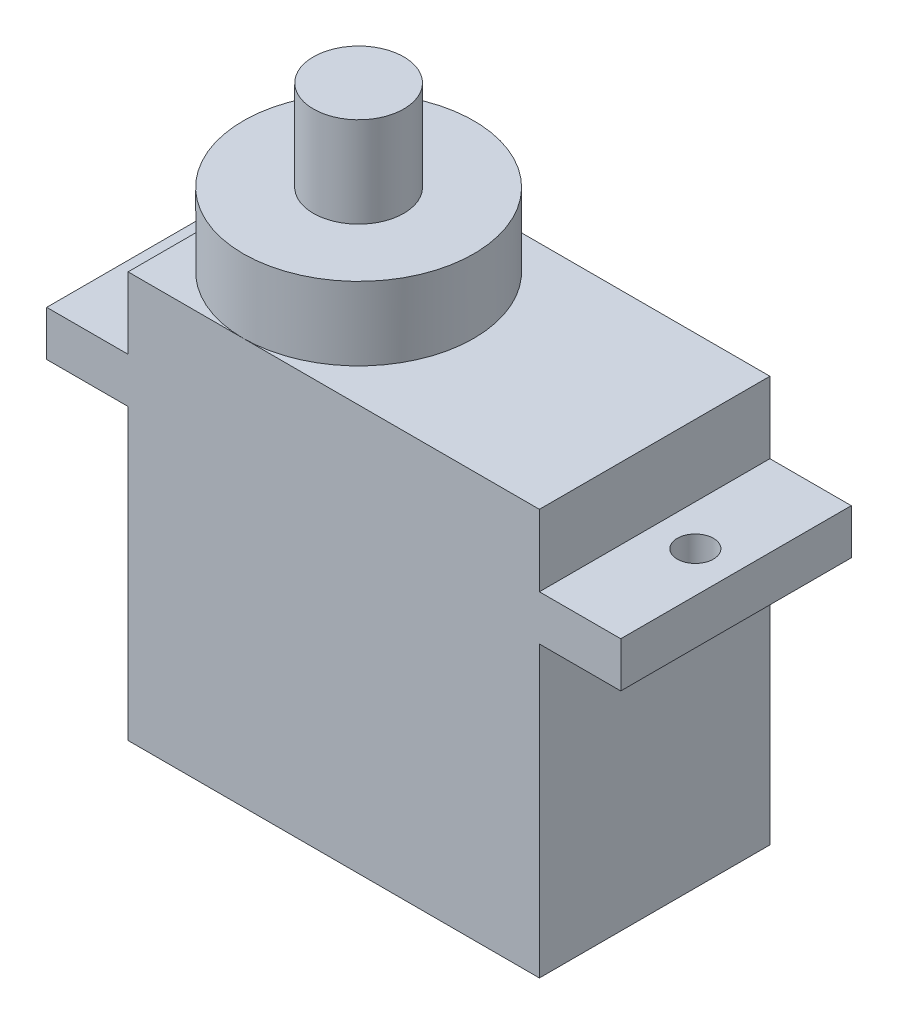
SolidWorks part; units mm, degrees
ref_plane "Front Plane" through (0, 0, 0) normal (0, 0, 1) x (1, 0, 0)
ref_plane "Top Plane" through (0, 0, 0) normal (0, 1, 0) x (1, 0, 0)
ref_plane "Right Plane" through (0, 0, 0) normal (1, 0, 0) x (0, 0, -1)
sketch "Sketch1" plane through (0, 0, 0) normal (0, 0, 1) x (1, 0, 0)
  line L1 (-7.8959, -11.225) -> (14.8541, -11.225)
  line L2 (-7.8959, -11.225) -> (-7.8959, 11.225)
  line L3 (-7.8959, 11.225) -> (14.8541, 11.225)
  line L4 (14.8541, -11.225) -> (14.8541, 11.225)
  point P0 (0, 0)
  dimension "D1" = 22.45
  dimension "D2" = 22.75
extrude "Boss-Extrude1" add sketch "Sketch1" along normal blind 12.75
sketch "Sketch2" plane through (14.8541, 0, 0) normal (1, 0, 0) x (0, 0, -1)
  line L0 (-12.75, -11.225) -> (-12.75, 11.225) construction
  line L1 (-12.75, 7.275) -> (0, 7.275)
  line L2 (-12.75, 7.275) -> (-12.75, 4.775)
  line L3 (-12.75, 4.775) -> (0, 4.775)
  line L4 (0, 7.275) -> (0, 4.775)
  line L5 (0, -11.225) -> (0, 11.225) construction
  line L6 (-12.75, -11.225) -> (0, -11.225) construction
  dimension "D1" = 2.5
  dimension "D2" = 18.5
extrude "Boss-Extrude2" add sketch "Sketch2" along normal blind 4.5
sketch "Sketch3" plane through (-7.8959, 0, 0) normal (-1, 0, 0) x (0, 0, 1)
  line L0 (0, 11.225) -> (0, -11.225) construction
  line L1 (0, 7.275) -> (12.75, 7.275)
  line L2 (0, 7.275) -> (0, 4.775)
  line L3 (0, 4.775) -> (12.75, 4.775)
  line L4 (12.75, 7.275) -> (12.75, 4.775)
  line L5 (12.75, 11.225) -> (12.75, -11.225) construction
  line L6 (12.75, -11.225) -> (0, -11.225) construction
  dimension "D1" = 2.5
  dimension "D2" = 18.5
extrude "Boss-Extrude3" add sketch "Sketch3" along normal blind 4.5
sketch "Sketch4" plane through (0, 7.275, 0) normal (0, 1, 0) x (1, 0, 0)
  line L1 (-12.3959, 0) -> (-7.8959, 0) construction
  line L3 (-12.3959, -12.75) -> (-12.3959, 0) construction
  circle A0 centre (-10.1459, -6.375) radius 1
  dimension "D1" = 2
  dimension "D2" = 6.375
  dimension "D3" = 2.25
extrude "Cut-Extrude1" cut sketch "Sketch4" against normal blind 2.5
sketch "Sketch5" plane through (0, 7.275, 0) normal (0, 1, 0) x (1, 0, 0)
  line L0 (19.3541, 0) -> (19.3541, -12.75) construction
  line L1 (19.3541, -12.75) -> (14.8541, -12.75) construction
  circle A0 centre (17.1041, -6.375) radius 1
  dimension "D1" = 2
  dimension "D2" = 2.25
  dimension "D3" = 6.375
extrude "Cut-Extrude2" cut sketch "Sketch5" against normal blind 2.5
sketch "Sketch6" plane through (0, 11.225, 0) normal (0, 1, 0) x (1, 0, 0)
  line L0 (14.8541, 0) -> (-7.8959, 0) construction
  line L3 (-7.8959, -12.75) -> (-7.8959, 0) construction
  circle A0 centre (-1.5209, -6.375) radius 6.375
  dimension "D2" = 12.75
  dimension "D1" = 6.375
  dimension "D3" = 6.375
extrude "Boss-Extrude4" add sketch "Sketch6" along normal blind 4.05
sketch "Sketch7" plane through (0, 15.275, 0) normal (0, 1, 0) x (1, 0, 0)
  line L0 (-1.5209, 0) -> (-7.8959, 0) construction
  line L1 (-7.8959, -12.75) -> (-7.8959, 0) construction
  circle A0 centre (-1.5209, -6.375) radius 2.5
  dimension "D1" = 5
  dimension "D2" = 6.375
  dimension "D3" = 6.375
extrude "Boss-Extrude5" add sketch "Sketch7" along normal blind 5
